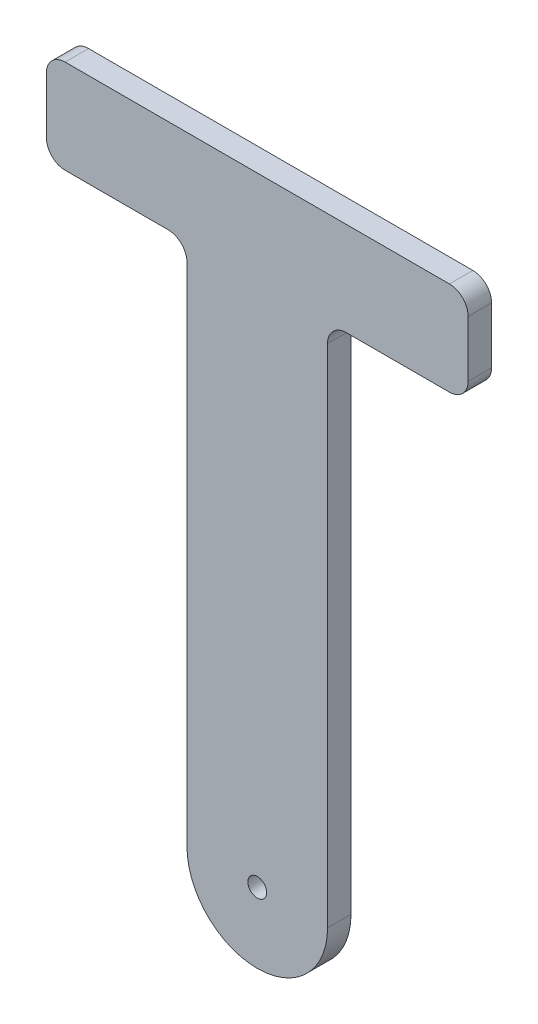
SolidWorks part; units mm, degrees
ref_plane "Front Plane" through (0, 0, 0) normal (0, 0, 1) x (1, 0, 0)
ref_plane "Top Plane" through (0, 0, 0) normal (0, 1, 0) x (1, 0, 0)
ref_plane "Right Plane" through (0, 0, 0) normal (1, 0, 0) x (0, 0, -1)
sketch "Sketch1" plane through (0, 0, 0) normal (0, 0, 1) x (1, 0, 0)
  line L0 (-19.353, 0) -> (-19.353, 68.58)
  line L2 (-0.303, 68.58) -> (-0.303, 0)
  line L4 (-21.893, 71.12) -> (-35.863, 71.12)
  line L5 (-38.403, 73.66) -> (-38.403, 81.28)
  line L6 (2.237, 71.12) -> (16.207, 71.12)
  line L7 (18.747, 73.66) -> (18.747, 81.28)
  line L8 (16.207, 83.82) -> (-35.863, 83.82)
  arc A1 (-19.353, 0) -> (-0.303, 0) centre (-9.828, 0) ccw
  circle A2 centre (-9.828, 0) radius 1.27
  arc A4 (2.237, 71.12) -> (-0.303, 68.58) centre (2.237, 68.58) ccw
  arc A5 (-19.353, 68.58) -> (-21.893, 71.12) centre (-21.893, 68.58) ccw
  arc A6 (16.207, 71.12) -> (18.747, 73.66) centre (16.207, 73.66) ccw
  arc A7 (18.747, 81.28) -> (16.207, 83.82) centre (16.207, 81.28) ccw
  arc A8 (-38.403, 81.28) -> (-35.863, 83.82) centre (-35.863, 81.28) cw
  arc A9 (-35.863, 71.12) -> (-38.403, 73.66) centre (-35.863, 73.66) cw
  dimension "D3" = 2.54
  dimension "D6" = 2.54
  dimension "D4" = 19.05
extrude "Boss-Extrude1" add sketch "Sketch1" along normal blind 3.175
